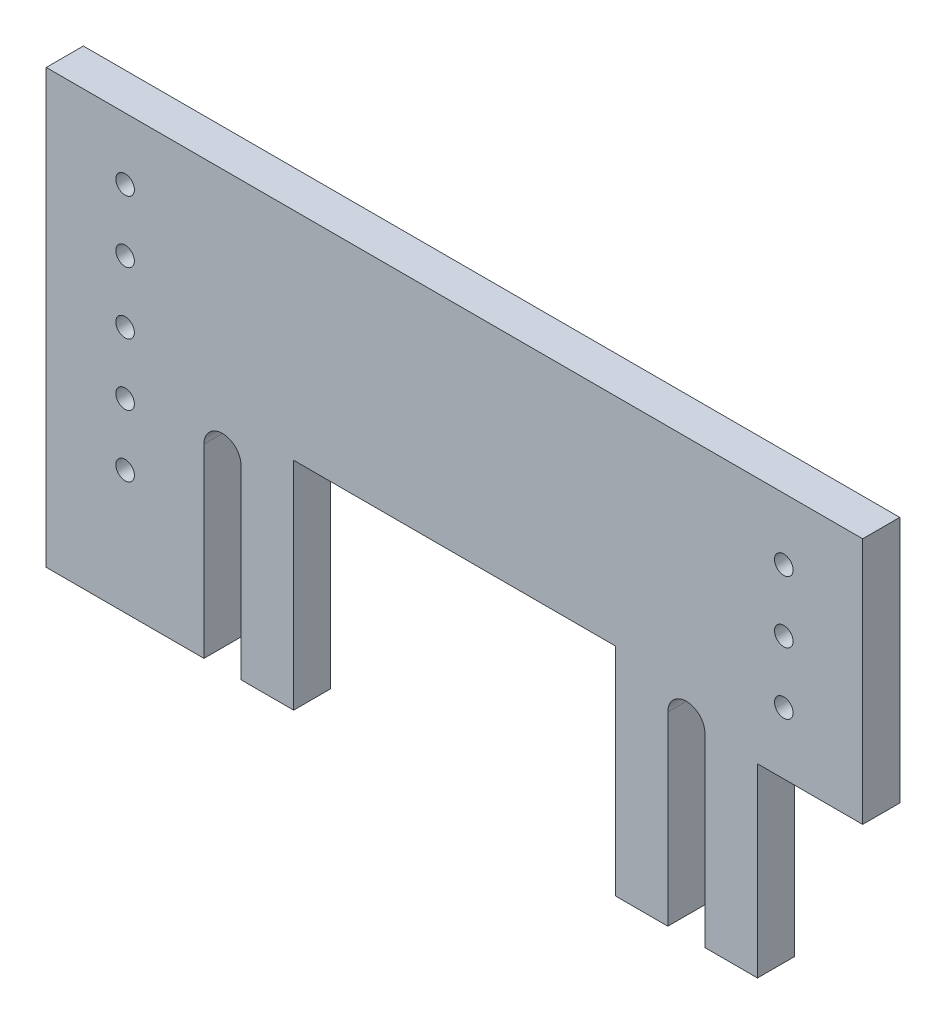
SolidWorks part; units mm, degrees
material "Balsa"
ref_plane "Plano frontal" through (0, 0, 0) normal (0, 0, 1) x (1, 0, 0)
ref_plane "Plano superior" through (0, 0, 0) normal (0, 1, 0) x (1, 0, 0)
ref_plane "Plano direito" through (0, 0, 0) normal (1, 0, 0) x (0, 0, -1)
sketch "Esboço1" plane through (0, 0, 0) normal (0, 0, 1) x (1, 0, 0)
  line L0 (-66, -35) -> (-40.5, -35)
  line L1 (40.5, -35) -> (49, -35)
  line L2 (66, -5) -> (66, 35)
  line L3 (66, 35) -> (-66, 35)
  line L4 (-66, -35) -> (-66, 35)
  line L5 (49, -25.9848) -> (-66, 35) construction
  line L6 (66, 35) -> (-66, -35) construction
  line L7 (34.5, -35) -> (26, -35)
  line L8 (34.5, -5) -> (34.5, -35)
  line L9 (40.5, -5) -> (40.5, -35)
  line L10 (-40.5, -5) -> (-40.5, -35)
  line L11 (-34.5, -5) -> (-34.5, -35)
  line L12 (-26, -35) -> (-34.5, -35)
  line L13 (0, 0) -> (0, -26.3908) construction
  line L14 (26, -35) -> (26, 0)
  line L15 (26, 0) -> (-26, 0)
  line L16 (-26, -35) -> (-26, 0)
  line L17 (49, -35) -> (49, -5)
  line L18 (49, -5) -> (66, -5)
  arc A0 (-34.5, -5) -> (-40.5, -5) centre (-37.5, -5) ccw
  arc A1 (40.5, -5) -> (34.5, -5) centre (37.5, -5) ccw
  circle A2 centre (-53.25, -5) radius 1.5
  circle A3 centre (-53.25, -15) radius 1.5
  circle A4 centre (-53.25, 15) radius 1.5
  circle A5 centre (-53.25, 25) radius 1.5
  circle A6 centre (-53.25, 5) radius 1.5
  circle A7 centre (53.25, 5) radius 1.5
  circle A8 centre (53.25, 25) radius 1.5
  circle A9 centre (53.25, 15) radius 1.5
  point P0 (0, 0)
  point P2 (0, 0)
  point P32 (-53.25, -35)
  point P40 (49.8243, -8.3958)
  point P46 (0, 35)
  point P47 (0, 0)
  dimension "D1" = 8.5
  dimension "D15" = 3
  dimension "D5" = 10
  dimension "D2" = 75
  dimension "D3" = 35
  dimension "D4" = 25.5
  dimension "D6" = 6
  dimension "D7" = 30
  dimension "D8" = 132
  dimension "D9" = 10
  dimension "D10" = 70
  dimension "D11" = 30
  dimension "D14" = 10
  dimension "D16" = 10
  dimension "D17" = 10
extrude "Ressalto-extrusão1" add sketch "Esboço1" along normal blind 6
